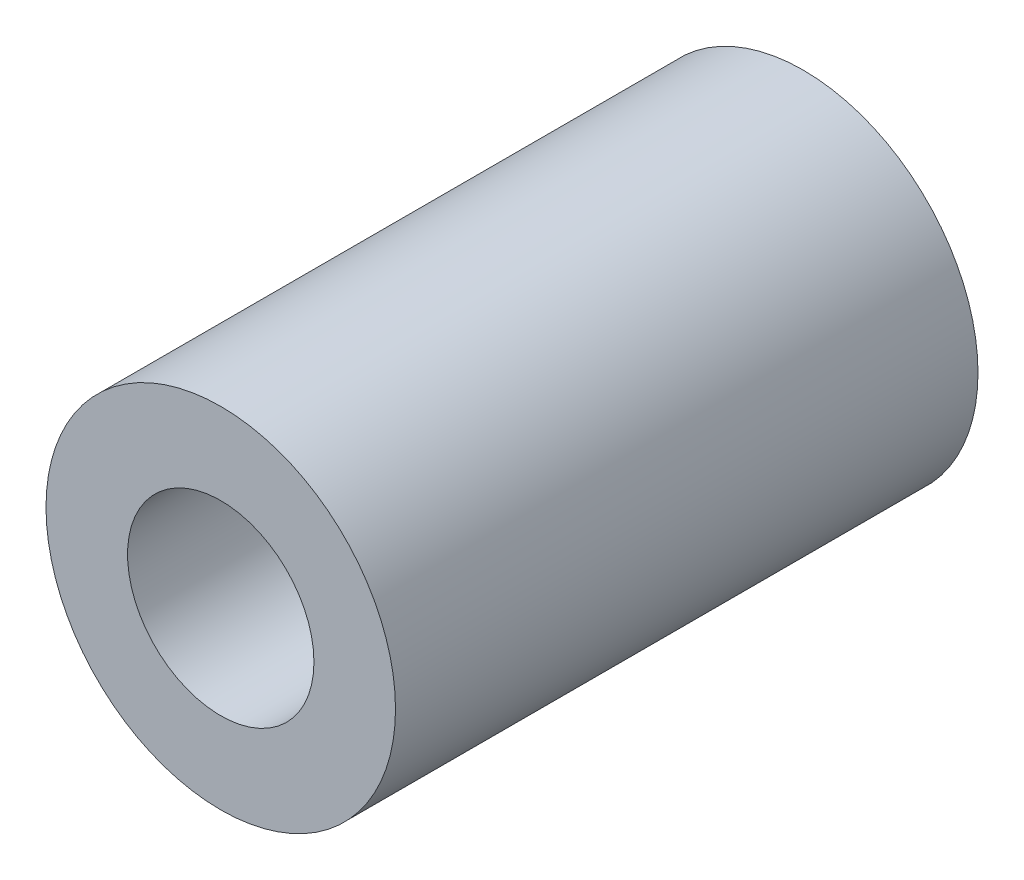
SolidWorks part; units mm, degrees
ref_plane "Front Plane" through (0, 0, 0) normal (0, 0, 1) x (1, 0, 0)
ref_plane "Top Plane" through (0, 0, 0) normal (0, 1, 0) x (1, 0, 0)
ref_plane "Right Plane" through (0, 0, 0) normal (1, 0, 0) x (0, 0, -1)
sketch "Sketch1" plane through (0, 0, 0) normal (0, 0, 1) x (1, 0, 0)
  circle A0 centre (0, 0) radius 3
  circle A1 centre (0, 0) radius 1.6
  dimension "OD" = 6
  dimension "ID" = 3.2
extrude "Extrude1" add sketch "Sketch1" along normal mid plane 10
sketch "Sketch2" plane through (0, 0, 0) normal (1, 0, 0) x (0, 0, -1)
  line L0 (-5, -1.6) -> (5, -1.6) construction
  line L3 (5, 1.6) -> (-5, 1.6) construction
  line L5 (-5, -1.6) -> (5, -1.6)
  line L6 (5, 1.6) -> (-5, 1.6)
sketch "Sketch4" plane through (0, 0, 5) normal (0, 0, 1) x (1, 0, 0)
  line L0 (0, 0) -> (-1.1314, 1.1314)
  line L1 (0, -1.1) -> (0, 1.1) construction
  circle A0 centre (0, 0) radius 1.6 construction
  dimension "D1" = 45
